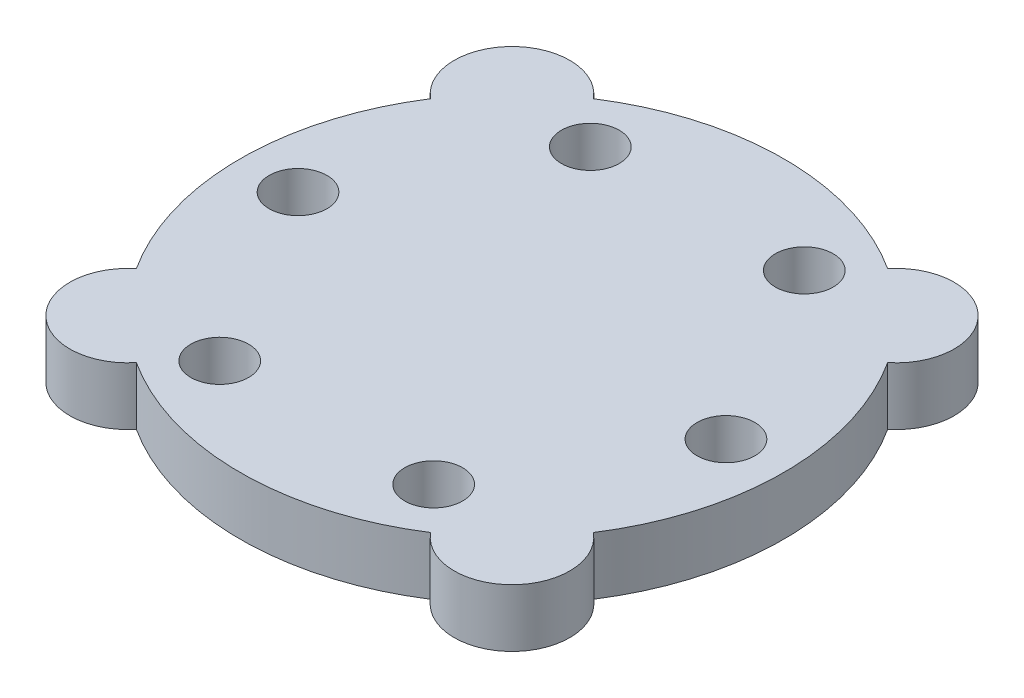
SolidWorks part; units mm, degrees
material "Polybutadiene (PB)"
ref_plane "Front" through (0, 0, 0) normal (0, 0, 1) x (1, 0, 0)
ref_plane "Top" through (0, 0, 0) normal (0, 1, 0) x (1, 0, 0)
ref_plane "Right" through (0, 0, 0) normal (1, 0, 0) x (0, 0, -1)
sketch "Sketch1" plane through (0, 0, 0) normal (0, 1, 0) x (1, 0, 0)
  line L0 (-1.6617, 1.6617) -> (1.6617, -1.6617) construction
  line L1 (-1.6617, -1.6617) -> (1.6617, 1.6617) construction
  line L2 (-2.35, 0) -> (2.35, 0) construction
  circle A0 centre (0, 0) radius 2.85 construction
  arc A1 (-1.9756, 1.2725) -> (-1.9756, -1.2725) centre (0, 0) ccw
  arc A2 (-1.9756, -1.2725) -> (-1.2725, -1.9756) centre (-1.6617, -1.6617) ccw
  arc A3 (-1.2725, 1.9756) -> (-1.9756, 1.2725) centre (-1.6617, 1.6617) ccw
  arc A4 (1.9756, 1.2725) -> (1.2725, 1.9756) centre (1.6617, 1.6617) ccw
  arc A5 (1.2725, -1.9756) -> (1.9756, -1.2725) centre (1.6617, -1.6617) ccw
  arc A6 (-1.2725, -1.9756) -> (1.2725, -1.9756) centre (0, 0) ccw
  arc A7 (1.9756, -1.2725) -> (1.9756, 1.2725) centre (0, 0) ccw
  arc A8 (1.2725, 1.9756) -> (-1.2725, 1.9756) centre (0, 0) ccw
  dimension "D1" = 5.7
  dimension "D2" = 4.7
  dimension "D3" = 45
extrude "Boss-Extrude1" add sketch "Sketch1" along normal mid plane 0.5
sketch "Sketch2" plane through (0, 0.25, 0) normal (0, 1, 0) x (1, 0, 0)
  circle A0 centre (-1.85, 0) radius 0.25
  circle A1 centre (0, 0) radius 1.85 construction
  circle A2 centre (-0.925, 1.6021) radius 0.25
  circle A3 centre (0.925, 1.6021) radius 0.25
  circle A4 centre (1.85, 0) radius 0.25
  circle A5 centre (0.925, -1.6021) radius 0.25
  circle A6 centre (-0.925, -1.6021) radius 0.25
  point P18 (0, 0)
  dimension "D1" = 0.5
  dimension "D2" = 3.7
  dimension "D3" = 6
extrude "Cut-Extrude1" cut sketch "Sketch2" against normal up to next
